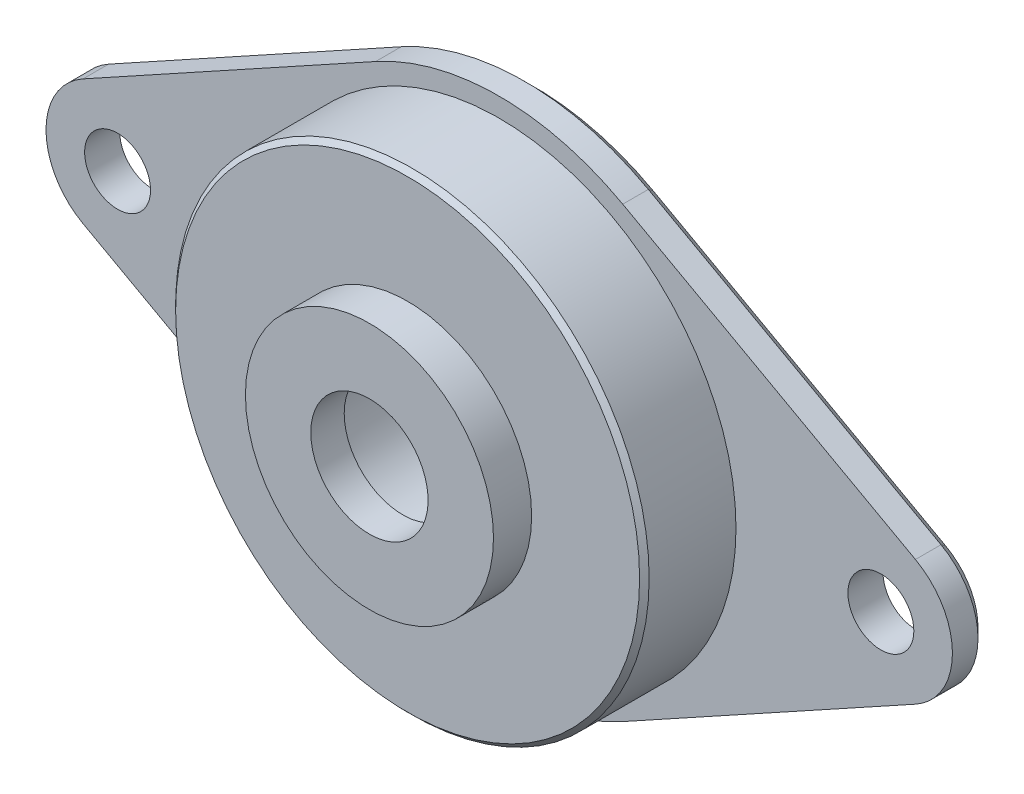
SolidWorks part; units mm, degrees
material "Brass"
ref_plane "Front" through (0, 0, 0) normal (0, 0, 1) x (1, 0, 0)
ref_plane "Top" through (0, 0, 0) normal (0, 1, 0) x (1, 0, 0)
ref_plane "Right" through (0, 0, 0) normal (1, 0, 0) x (0, 0, -1)
sketch "Sketch1" plane through (0, 0, 0) normal (0, 1, 0) x (1, 0, 0)
  line L0 (0, 0) -> (12.4079, 0)
  line L1 (13.4079, 6.64) -> (13.4079, 4.8)
  line L2 (13.4079, 4.8) -> (12.4079, 4.8)
  line L3 (12.4079, 4.8) -> (12.4079, 0)
  line L6 (13.4079, 6.64) -> (0, 6.64)
  line L7 (0, 6.64) -> (0, 0)
  line L8 (0, 0) -> (0, 31.3021) construction
  dimension "D1" = 1.84
  dimension "D2" = 4.8
  dimension "D3" = 24.8158
  dimension "D4" = 1
revolve "Revolve1" add sketch "Sketch1" angle 360 about L8
sketch "Sketch2" plane through (0, 0, 0) normal (0, 0, 1) x (1, 0, 0)
  circle A0 centre (0, 0) radius 6.5
  dimension "D1" = 13
extrude "Boss-Extrude1" add sketch "Sketch2" along normal blind 2
sketch "Sketch3" plane through (0, 0, -6.64) normal (0, 0, -1) x (-1, 0, 0)
  line L0 (0, 0) -> (-20, 0) construction
  line L1 (0, 0) -> (0, -6.194) construction
  line L2 (-21.8109, -3.2838) -> (-6.4746, -11.741)
  line L3 (-21.8109, 3.2838) -> (-6.4746, 11.741)
  circle A0 centre (-20, 0) radius 6.35 construction
  arc A2 (-21.8109, 3.2838) -> (-21.8109, -3.2838) centre (-20, 0) ccw
  arc A3 (-6.4746, 11.741) -> (-6.4746, -11.741) centre (0, 0) ccw
  circle A4 centre (0, 0) radius 13.4079 construction
  dimension "D1" = 12.7
  dimension "D2" = 7.5
  dimension "D3" = 40
extrude "Boss-Extrude2" add sketch "Sketch3" against normal up to surface (1.84 mm away) up to face at (13.4079, 0, -4.8)
hole_wizard "#4 Clearance Hole1" positions "Sketch5" profile "Sketch4" hole size "#4" standard "Ansi Inch"
sketch "Sketch5" plane through (0, 0, -6.64) normal (0, 0, -1) x (-1, 0, 0)
  arc A0 (-21.8109, 3.2838) -> (-21.8109, -3.2838) centre (-20, 0) ccw construction
  point P0 (-20, 0)
sketch "Sketch4" plane through (20, 0, -6.64) normal (1, 0, 0) x (0, 1, 0)
  line L0 (0, 0) -> (0, 16.0378)
  line L1 (0, 16.0378) -> (1.7272, 15)
  line L2 (1.7272, 15) -> (1.7272, 0)
  line L5 (1.7272, 0) -> (0, 0)
  line L10 (0, 16.0378) -> (-1.7272, 15) construction
  line L11 (0, -6.35) -> (0, 107.95) construction
  dimension "Hole Dia." = 3.4544
  dimension "Hole Depth" = 15
  dimension "Drill Angle" = 118
mirror "Mirror1" about plane through (0, 0, 0) normal (1, 0, 0) of "#4 Clearance Hole1", "Boss-Extrude2"
hole_wizard "1/16 NPT Tapped Hole2" positions "Sketch9" profile "Sketch8" size "1/16" standard "Ansi Inch" end condition through all
sketch "Sketch9" plane through (0, 0, -6.64) normal (0, 0, -1) x (-1, 0, 0)
  arc A1 (6.4746, 11.741) -> (-6.4746, 11.741) centre (0, 0) ccw construction
  point P0 (0, 0)
sketch "Sketch8" plane through (0, 0, -6.64) normal (1, 0, 0) x (0, 1, 0)
  line L0 (0, 0) -> (0, 8.64)
  line L1 (0, 8.64) -> (3.0734, 8.64)
  line L3 (3.0734, 8.64) -> (3.0734, 6.89)
  line L4 (3.0734, 6.89) -> (3.7816, 6.89)
  line L5 (3.7816, 6.89) -> (3.9689, 0.635)
  line L6 (3.9689, 0.635) -> (4.6039, 0)
  line L7 (4.6039, 0) -> (0, 0)
  line L8 (0, -6.35) -> (0, 107.95) construction
  line L9 (-3.9689, 0.635) -> (-4.6039, 0) construction
  line L11 (-3.0734, 6.89) -> (-3.7816, 6.89) construction
  line L12 (-3.7816, 6.89) -> (-3.9689, 0.635) construction
  dimension "Thru Tap Drill Dia." = 6.1468
  dimension "Thru Tap Drill Depth" = 8.64
  dimension "Thread Dia." = 7.9378
  dimension "Thread Angle" = 3.43
  dimension "Thread Depth" = 6.89
  dimension "Near C'Sink Dia." = 9.2078
  dimension "Near C'Sink Angle" = 90
chamfer "Chamfer1" distance 0.25 angle 45 1 edges at (12.4079, 0, 0)
chamfer "Chamfer2" distance 0.5 angle 45 8 edges at (0, 13.4079, -6.64) (14.1427, 7.5124, -6.64) (-14.1427, 7.5124, -6.64) (23.75, 0, -6.64) (-23.75, 0, -6.64) (-14.1427, -7.5124, -6.64) (0, -13.4079, -6.64) (14.1427, -7.5124, -6.64)
